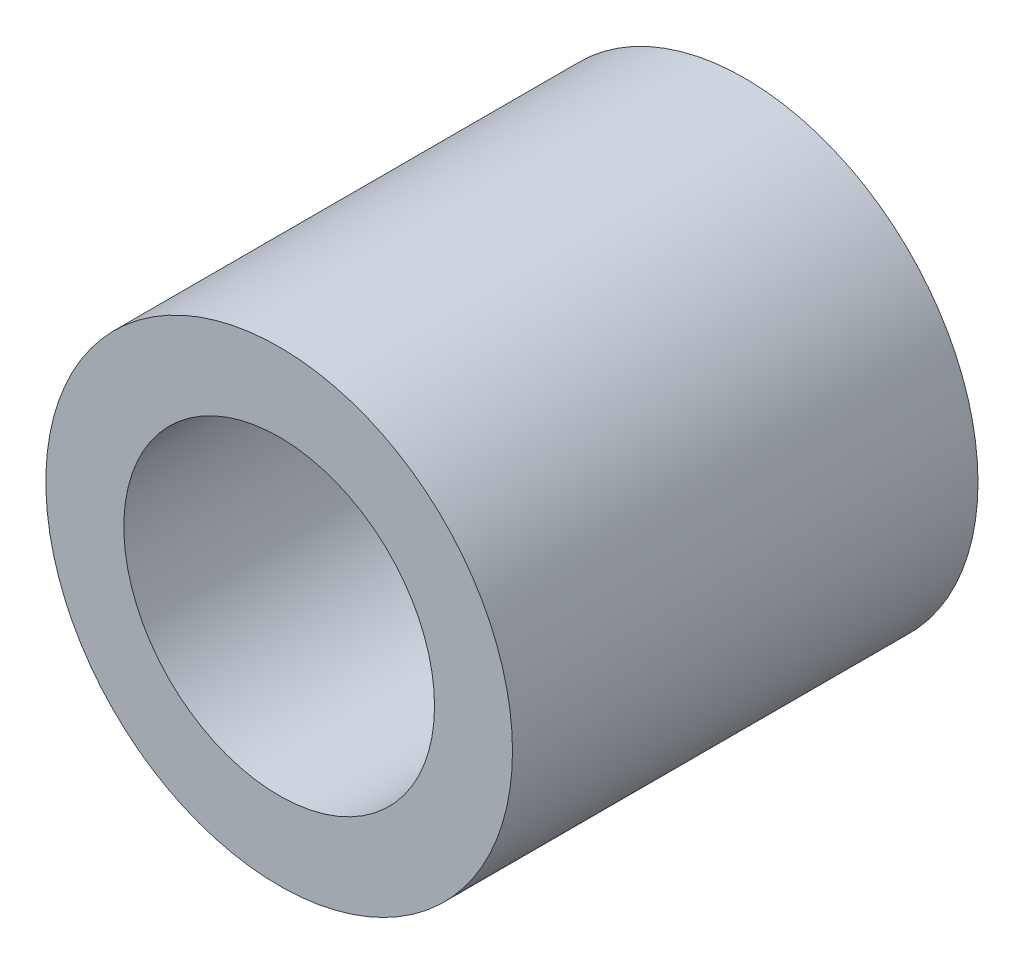
SolidWorks part; units mm, degrees
ref_plane "Front Plane" through (0, 0, 0) normal (0, 0, 1) x (1, 0, 0)
ref_plane "Top Plane" through (0, 0, 0) normal (0, 1, 0) x (1, 0, 0)
ref_plane "Right Plane" through (0, 0, 0) normal (1, 0, 0) x (0, 0, -1)
sketch "Sketch1" plane through (0, 0, 0) normal (0, 0, 1) x (1, 0, 0)
  circle A0 centre (0, 0) radius 6.015
  circle A1 centre (0, 0) radius 4.005
  dimension "D1" = 12.03
  dimension "ID" = 8.01
extrude "Extrude1" add sketch "Sketch1" along normal mid plane 12
sketch "Sketch2" plane through (0, 0, 0) normal (1, 0, 0) x (0, 0, -1)
  line L0 (-6, -4.005) -> (6, -4.005) construction
  line L3 (6, 4.005) -> (-6, 4.005) construction
  line L5 (-6, -4.005) -> (6, -4.005)
  line L6 (6, 4.005) -> (-6, 4.005)
sketch "Sketch4" plane through (0, 0, 6) normal (0, 0, 1) x (1, 0, 0)
  line L0 (0, 0) -> (-2.832, 2.832)
  line L1 (0, -5.5) -> (0, 5.5) construction
  circle A0 centre (0, 0) radius 4.005 construction
  dimension "D1" = 45
